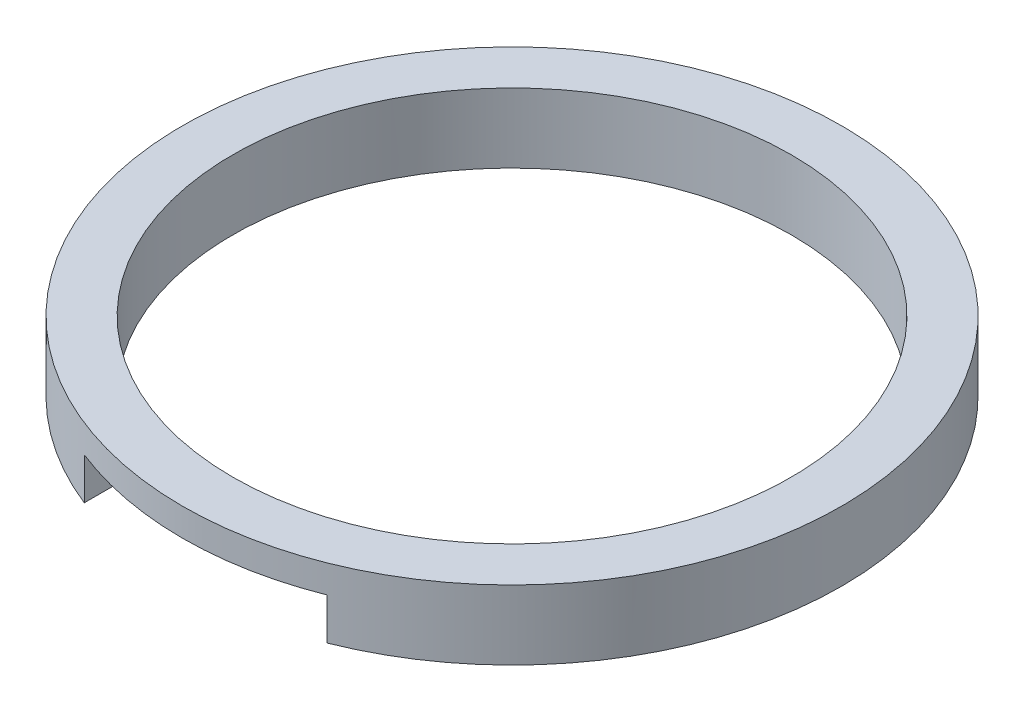
SolidWorks part; units mm, degrees
ref_plane "Front Plane" through (0, 0, 0) normal (0, 0, 1) x (1, 0, 0)
ref_plane "Top Plane" through (0, 0, 0) normal (0, 1, 0) x (1, 0, 0)
ref_plane "Right Plane" through (0, 0, 0) normal (1, 0, 0) x (0, 0, -1)
sketch "Sketch1" plane through (0, 0, 0) normal (0, 1, 0) x (1, 0, 0)
  circle A0 centre (0, 0) radius 9.5
  dimension "D1" = 19
extrude "Boss-Extrude1" add sketch "Sketch1" along normal blind 2
sketch "Sketch2" plane through (0, 2, 0) normal (0, 1, 0) x (1, 0, 0)
  circle A0 centre (0, 0) radius 8.05
  dimension "D1" = 16.1
extrude "Cut-Extrude1" cut sketch "Sketch2" against normal through all
sketch "Sketch3" plane through (0, 0, 0) normal (0, -1, 0) x (1, 0, 0)
  line L0 (0, 0) -> (0, 9.5) construction
  line L3 (-3.5, 7.2493) -> (-3.5, 8.8318)
  line L5 (3.5, 7.2493) -> (3.5, 8.8318)
  circle A0 centre (0, 0) radius 9.5 construction
  circle A1 centre (0, 0) radius 8.05 construction
  arc A2 (3.5, 8.8318) -> (-3.5, 8.8318) centre (0, 0) ccw
  arc A3 (3.5, 7.2493) -> (-3.5, 7.2493) centre (0, 0) ccw
  point P3 (0, 6.9961)
  point P4 (0, 8.05)
  dimension "D1" = 7
extrude "Cut-Extrude2" cut sketch "Sketch3" against normal blind 1.2
